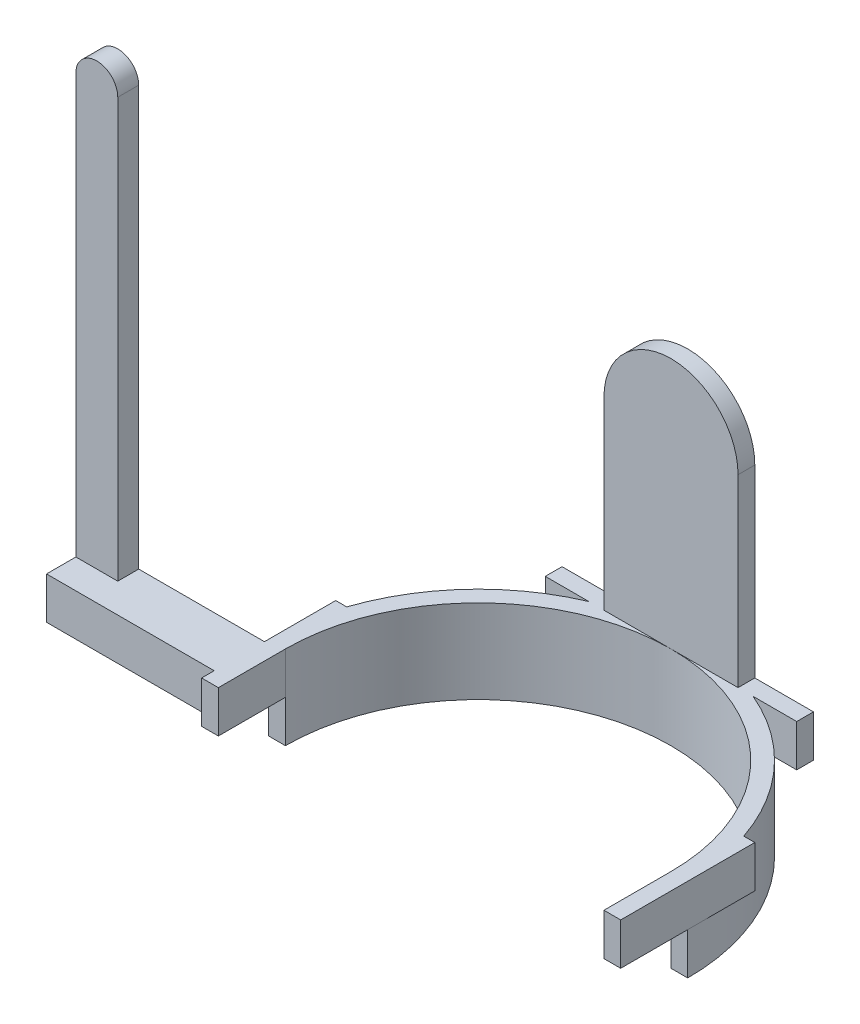
SolidWorks part; units mm, degrees
ref_plane "Front" through (0, 0, 0) normal (0, 0, 1) x (1, 0, 0)
ref_plane "Top" through (0, 0, 0) normal (0, 1, 0) x (1, 0, 0)
ref_plane "Right" through (0, 0, 0) normal (1, 0, 0) x (0, 0, -1)
sketch "草图1" plane through (0, 0, 0) normal (0, 1, 0) x (1, 0, 0)
  line L0 (-39.7033, 0) -> (64.2421, 0) construction
  line L1 (-50, 0) -> (-46, 0)
  line L2 (46, 0) -> (50, 0)
  arc A0 (-50, 0) -> (50, 0) centre (0, 0) cw
  arc A1 (-46, 0) -> (46, 0) centre (0, 0) cw
extrude "凸台-拉伸1" add sketch "草图1" along normal blind 10
sketch "草图3" plane through (0, 10, 0) normal (0, 1, 0) x (1, 0, 0)
  line L0 (46, 0) -> (50, 0) construction
  line L1 (-50, 0) -> (-46, 0) construction
  line L2 (-50, 16) -> (-47.3709, 16)
  line L3 (-50, 16) -> (-50, -16)
  line L4 (-50, -16) -> (-46, -16)
  line L5 (-46, 0) -> (-46, -16)
  line L6 (50, 16) -> (47.3709, 16)
  line L7 (50, 16) -> (50, -16)
  line L8 (50, -16) -> (46, -16)
  line L9 (46, 0) -> (46, -16)
  line L10 (0, 0) -> (0, 56.0177) construction
  line L11 (-26.9117, 46) -> (-19.5959, 46) construction
  line L12 (-22.8935, 50) -> (37.5767, 50) construction
  line L13 (19.5959, 46) -> (38.2628, 46) construction
  line L14 (-30, 50) -> (30, 50)
  line L15 (-30, 50) -> (-30, 46)
  line L16 (-30, 46) -> (-19.5959, 46)
  line L17 (30, 50) -> (30, 46)
  line L18 (19.5959, 46) -> (30, 46)
  arc A0 (-47.3709, 16) -> (-19.5959, 46) centre (0, 0) cw
  arc A1 (-46, 0) -> (46, 0) centre (0, 0) cw
  arc A2 (19.5959, 46) -> (47.3709, 16) centre (0, 0) cw
  dimension "D1" = 32
  dimension "D2" = 16
  dimension "D3" = 32
  dimension "D4" = 16
  dimension "D5" = 60
  dimension "D6" = 30
extrude "凸台-拉伸2" add sketch "草图3" along normal blind 10
sketch "草图4" plane through (0, 20, 0) normal (0, 1, 0) x (1, 0, 0)
  line L5 (0, 50) -> (0, 35.5033) construction
  line L6 (30, 50) -> (-30, 50) construction
  line L8 (-16, 50) -> (16, 50)
  line L9 (-16, 50) -> (-16, 46)
  line L10 (-16, 46) -> (16, 46)
  line L11 (16, 50) -> (16, 46)
  dimension "D1" = 16
  dimension "D2" = 16
extrude "凸台-拉伸3" add sketch "草图4" along normal blind 60
sketch "草图5" plane through (0, 0, -50) normal (0, 0, -1) x (-1, 0, 0)
  line L2 (-16, 64) -> (-16, 97.9053)
  line L3 (-16, 97.9053) -> (16, 97.9053)
  line L4 (16, 64) -> (16, 97.9053)
  arc A0 (16, 64) -> (-16, 64) centre (0, 64) ccw
extrude "切除-拉伸1" cut sketch "草图5" against normal blind 30
sketch "草图6" plane through (-50, 0, 0) normal (-1, 0, 0) x (0, 0, 1)
  line L0 (-16, 20) -> (16, 20) construction
  line L1 (1, 20) -> (13, 20)
  line L2 (1, 20) -> (1, 10)
  line L3 (1, 10) -> (13, 10)
  line L4 (13, 20) -> (13, 10)
  line L5 (0, 10) -> (16, 10) construction
  line L6 (0, 10) -> (0, 0) construction
  dimension "D1" = 12
  dimension "D2" = 13
extrude "凸台-拉伸4" add sketch "草图6" along normal blind 40
sketch "草图7" plane through (0, 20, 0) normal (0, 1, 0) x (1, 0, 0)
  line L1 (-90, -1) -> (-80, -1)
  line L2 (-90, -1) -> (-90, -6)
  line L3 (-90, -6) -> (-80, -6)
  line L4 (-80, -1) -> (-80, -6)
  dimension "D1" = 10
extrude "凸台-拉伸5" add sketch "草图7" along normal blind 100
sketch "草图9" plane through (0, 0, 6) normal (0, 0, 1) x (1, 0, 0)
  line L0 (-90, 120) -> (-80, 120) construction
  circle A0 centre (-85, 120) radius 5
extrude "凸台-拉伸7" add sketch "草图9" against normal blind 5
